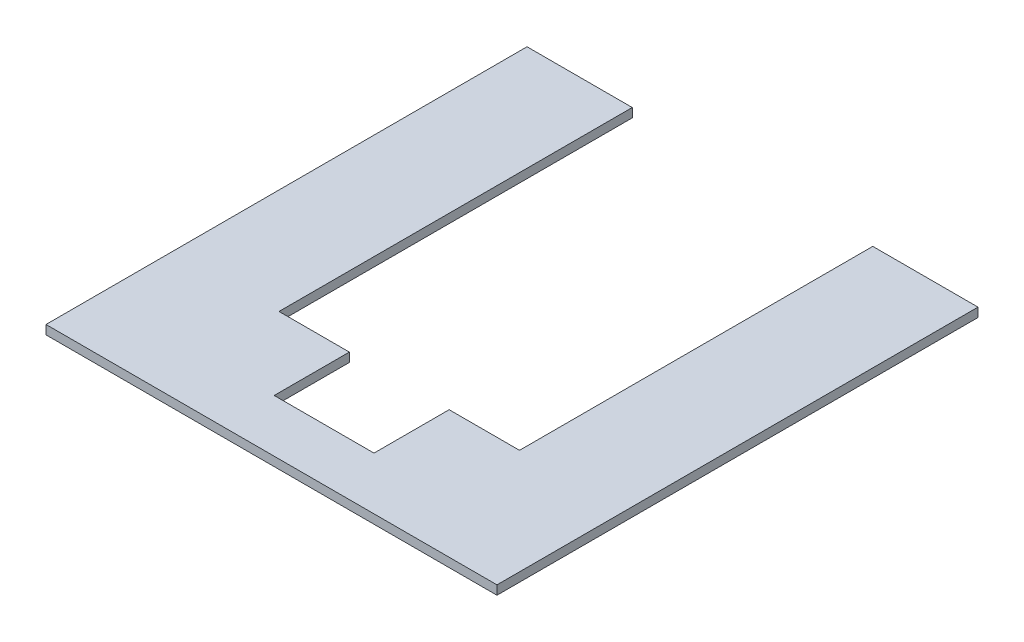
SolidWorks part; units mm, degrees
ref_plane "Front Plane" through (0, 0, 0) normal (0, 0, 1) x (1, 0, 0)
ref_plane "Top Plane" through (0, 0, 0) normal (0, 1, 0) x (1, 0, 0)
ref_plane "Right Plane" through (0, 0, 0) normal (1, 0, 0) x (0, 0, -1)
sketch "Sketch3" plane through (0, 0, 0) normal (0, 1, 0) x (1, 0, 0)
  line L1 (-75, 75) -> (75, 75)
  line L2 (-75, 75) -> (-75, -75)
  line L3 (-75, -75) -> (75, -75)
  line L4 (75, 75) -> (75, -75)
  line L5 (-75, 75) -> (75, -75) construction
  line L6 (-75, -75) -> (75, 75) construction
  point P0 (0, 0)
  dimension "D1" = 150
  dimension "D2" = 150
extrude "Boss-Extrude1" add sketch "Sketch3" along normal blind 3
sketch "Sketch4" plane through (0, 3, 0) normal (0, 1, 0) x (1, 0, 0)
  line L0 (75, 75) -> (-75, 75) construction
  line L1 (-40, 75) -> (40, 75)
  line L2 (-40, 75) -> (-40, -5)
  line L3 (-40, -5) -> (40, -5)
  line L4 (40, 75) -> (40, -5)
  line L5 (-75, 75) -> (-75, -75) construction
  dimension "D1" = 35
  dimension "D2" = 80
extrude "Cut-Extrude1" cut sketch "Sketch4" against normal blind 3
sketch "Sketch5" plane through (0, 0, -75) normal (0, 0, -1) x (-1, 0, 0)
  line L1 (-75, 3) -> (-40, 3)
  line L2 (-75, 3) -> (-75, 0)
  line L3 (-75, 0) -> (-40, 0)
  line L4 (-40, 3) -> (-40, 0)
  line L5 (40, 3) -> (75, 3)
  line L6 (40, 3) -> (40, 0)
  line L7 (40, 0) -> (75, 0)
  line L8 (75, 3) -> (75, 0)
extrude "Boss-Extrude2" add sketch "Sketch5" along normal blind 10
sketch "Sketch7" plane through (0, 0, 5) normal (0, 0, -1) x (-1, 0, 0)
  line L1 (-40, 3) -> (40, 3)
  line L2 (-40, 3) -> (-40, 0)
  line L3 (-40, 0) -> (40, 0)
  line L4 (40, 3) -> (40, 0)
extrude "Cut-Extrude2" cut sketch "Sketch7" against normal blind 27.5
sketch "Sketch8" plane through (0, 3, 0) normal (0, 1, 0) x (1, 0, 0)
  line L0 (-40, -32.5) -> (40, -32.5) construction
  line L1 (16.6, -32.5) -> (-16.6, -32.5)
  line L2 (16.6, -32.5) -> (16.6, -57.5)
  line L3 (16.6, -57.5) -> (-16.6, -57.5)
  line L4 (-16.6, -32.5) -> (-16.6, -57.5)
  line L5 (40, -32.5) -> (40, 85) construction
  dimension "D1" = 25
  dimension "D2" = 33.2
  dimension "D3" = 23.4
extrude "Cut-Extrude3" cut sketch "Sketch8" against normal blind 3
